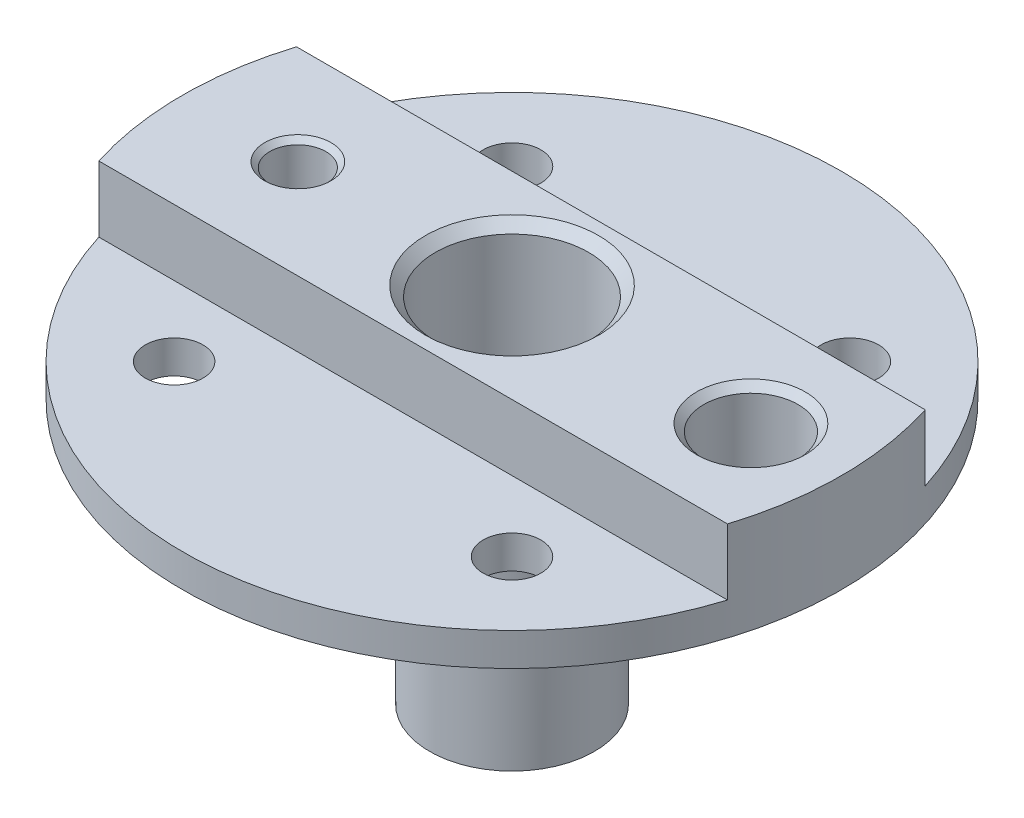
SolidWorks part; units mm, degrees
other "Markup1"
sketch "Sketch15" plane through (38, 45, 38) normal (0.9687, 0.1305, 0.2113) x (0.2474, -0.4357, -0.8654)
material "1.4305 (X8CrNiS18-9)"
ref_plane "Ebene vorne" through (0, 0, 0) normal (0, 0, 1) x (1, 0, 0)
ref_plane "Ebene oben" through (0, 0, 0) normal (0, 1, 0) x (1, 0, 0)
ref_plane "Ebene rechts" through (0, 0, 0) normal (1, 0, 0) x (0, 0, -1)
sketch "Sketch1" plane through (0, 0, 0) normal (0, 0, 1) x (1, 0, 0)
  line L0 (0, 0) -> (0, 46.1077) construction
  line L1 (-40, 44) -> (0, 44)
  line L2 (0, 8) -> (-7.5, 8)
  line L3 (-7.5, 8) -> (-7.5, 0)
  line L4 (-7.5, 0) -> (-10, 0)
  line L5 (-10, 0) -> (-10, 13)
  line L6 (-10, 13) -> (-10.1, 13)
  line L7 (-10.1, 13) -> (-10.1, 17)
  line L8 (-10.1, 17) -> (-9, 17)
  line L9 (-9, 17) -> (-9, 20)
  line L10 (-9, 20) -> (-12, 20)
  line L11 (-12, 20) -> (-12, 30)
  line L12 (-12, 30) -> (-14, 30)
  line L13 (-14, 30) -> (-14, 32)
  line L14 (-14, 32) -> (-40, 32)
  line L15 (-40, 32) -> (-40, 44)
  line L16 (0, 44) -> (0, 8)
  point P12 (-10.5, 20)
  point P20 (-9.55, 17)
  dimension "D1" = 20.2
  dimension "D2" = 20
  dimension "D3" = 18
  dimension "D4" = 2
  dimension "D5" = 2
  dimension "D6" = 40
  dimension "D7" = 12
  dimension "D8" = 12
  dimension "D9" = 1.5
  dimension "D10" = 24
  dimension "D11" = 3
  dimension "D12" = 4
  dimension "D13" = 8
  dimension "D14" = 17
revolve "Revolve1" add sketch "Sketch1" angle 360 about L0
hole_wizard "G1/2 Tapped Hole1" positions "Sketch2" profile "Sketch3" tap size "G1/2" standard "DIN"
sketch "Sketch2" plane through (0, 44, 0) normal (0, 1, 0) x (1, 0, 0)
  point P0 (0, 0)
sketch "Sketch3" plane through (0, 44, 0) normal (1, 0, 0) x (0, 0, 1)
  line L0 (0, 0) -> (0, 26.0373)
  line L1 (0, 26.0373) -> (9.3155, 20.44)
  line L2 (9.3155, 20.44) -> (9.3155, 1.187)
  line L3 (9.3155, 1.187) -> (10.5025, 0)
  line L5 (10.5025, 0) -> (0, 0)
  line L6 (-9.3155, 1.187) -> (-10.5025, 0) construction
  line L10 (0, 26.0373) -> (-9.3155, 20.44) construction
  line L11 (0, -6.35) -> (0, 107.95) construction
  dimension "Tap Drill Dia." = 18.631
  dimension "Tap Drill Depth" = 20.44
  dimension "Near C'Sink Dia." = 21.005
  dimension "Near C'Sink Angle" = 90
  dimension "Drill Angle" = 118
cosmetic thread "Hole Thread1" parameters "D1"=15, "D2"=20.955
ref_plane "Plane1" through (10.1, 0, 0) normal (1, 0, 0) x (0, 0, -1)
sketch "Sketch4" plane through (10.1, 0, 0) normal (1, 0, 0) x (0, 0, -1)
  line L0 (0, 17) -> (0, 13) construction
  line L1 (10.1, 17) -> (-10.1, 17) construction
  line L2 (-10, 13) -> (10, 13) construction
  line L3 (2, 17) -> (2, 13)
  line L4 (-2, 17) -> (-2, 13)
  arc A0 (2, 17) -> (-2, 17) centre (0, 17) ccw
  arc A1 (-2, 13) -> (2, 13) centre (0, 13) ccw
  point P6 (0, 15)
  dimension "D1" = 2
extrude "Cut-Extrude1" cut sketch "Sketch4" against normal blind 1
pattern_circular "CirPattern1" count 8 over 360 about axis through (0, 0, 0) along (0, 1, 0) of "Cut-Extrude1"
hole_wizard "G1/4 Tapped Hole1" positions "Sketch5" profile "Sketch6" tap size "G1/4" standard "DIN" end condition through all
sketch "Sketch5" plane through (0, 44, 0) normal (0, 1, 0) x (1, 0, 0)
  line L0 (0, 0) -> (29, 0) construction
  point P0 (29, 0)
  dimension "D1" = 29
sketch "Sketch6" plane through (29, 44, 0) normal (1, 0, 0) x (0, 0, 1)
  line L0 (0, 0) -> (0, 44)
  line L1 (0, 44) -> (5.7225, 44)
  line L2 (5.7225, 44) -> (5.7225, 0.881)
  line L3 (5.7225, 0.881) -> (6.6035, 0)
  line L5 (6.6035, 0) -> (0, 0)
  line L6 (-5.7225, 0.881) -> (-6.6035, 0) construction
  line L11 (0, -6.35) -> (0, 107.95) construction
  dimension "Thru Tap Drill Dia." = 11.445
  dimension "Thru Tap Drill Depth" = 44
  dimension "Near C'Sink Dia." = 13.207
  dimension "Near C'Sink Angle" = 90
cosmetic thread "Hole Thread2" parameters "D2"=13.157
hole_wizard "M6 Clearance Hole1" positions "Sketch7" profile "Sketch8" hole size "M6" standard "DIN" end condition through all
sketch "Sketch7" plane through (0, 44, 0) normal (0, 1, 0) x (1, 0, 0)
  line L0 (0, 0) -> (16.0639, 0) construction
  line L2 (0, 0) -> (20.5061, 20.5061) construction
  point P0 (20.5061, 20.5061)
  dimension "D1" = 29
  dimension "D2" = 45
sketch "Sketch8" plane through (20.5061, 44, -20.5061) normal (1, 0, 0) x (0, 0, 1)
  line L0 (0, 0) -> (0, 44)
  line L1 (0, 44) -> (3.5, 44)
  line L2 (3.5, 44) -> (3.5, 0.025)
  line L3 (3.5, 0.025) -> (3.525, 0)
  line L5 (3.525, 0) -> (0, 0)
  line L6 (-3.5, 0.025) -> (-3.525, 0) construction
  line L11 (0, -6.35) -> (0, 107.95) construction
  dimension "Thru Hole Dia." = 7
  dimension "Thru Hole Depth" = 44
  dimension "Near C'Sink Dia." = 7.05
  dimension "Near C'Sink Angle" = 90
pattern_circular "CirPattern2" count 4 over 360 about axis through (0, 0, 0) along (0, 1, 0) of "M6 Clearance Hole1"
hole_wizard "Ø2.5 (2.5) Diameter Hole1" positions "Sketch11" profile "Sketch12" hole size "Ø2.5" standard "DIN" end condition through all
sketch "Sketch11" plane through (0, 8, 0) normal (0, -1, 0) x (-1, 0, 0)
  point P0 (6, 0)
  dimension "D1" = 6
sketch "Sketch12" plane through (-6, 8, 0) normal (1, 0, 0) x (0, 0, -1)
  line L0 (0, 0) -> (0, 36)
  line L1 (0, 36) -> (1.25, 36)
  line L2 (1.25, 36) -> (1.25, 0.025)
  line L3 (1.25, 0.025) -> (1.275, 0)
  line L5 (1.275, 0) -> (0, 0)
  line L6 (-1.25, 0.025) -> (-1.275, 0) construction
  line L11 (0, -6.35) -> (0, 107.95) construction
  dimension "Thru Hole Dia." = 2.5
  dimension "Thru Hole Depth" = 36
  dimension "Near C'Sink Dia." = 2.55
  dimension "Near C'Sink Angle" = 90
pattern_circular "CirPattern3" count 8 over 360 about axis through (0, 0, 0) along (0, 1, 0) of "Ø2.5 (2.5) Diameter Hole1"
hole_wizard "M8 Tapped Hole2" positions "Sketch13" profile "Sketch14" tap size "M8" standard "DIN" end condition through all
sketch "Sketch13" plane through (0, 8, 0) normal (0, -1, 0) x (-1, 0, 0)
  point P0 (0, 0)
sketch "Sketch14" plane through (0, 8, 0) normal (1, 0, 0) x (0, 0, -1)
  line L0 (0, 0) -> (0, 36)
  line L1 (0, 36) -> (3.4, 36)
  line L2 (3.4, 36) -> (3.4, 0.625)
  line L3 (3.4, 0.625) -> (4.025, 0)
  line L5 (4.025, 0) -> (0, 0)
  line L6 (-3.4, 0.625) -> (-4.025, 0) construction
  line L11 (0, -6.35) -> (0, 107.95) construction
  dimension "Thru Tap Drill Dia." = 6.8
  dimension "Thru Tap Drill Depth" = 36
  dimension "Near C'Sink Dia." = 8.05
  dimension "Near C'Sink Angle" = 90
cosmetic thread "Hole Thread4" parameters "D2"=8
hole_wizard "M8 Tapped Hole3" positions "Sketch16" profile "Sketch17" tap size "M8" standard "DIN"
sketch "Sketch16" plane through (0, 44, 0) normal (0, 1, 0) x (1, 0, 0)
  line L0 (0, 0) -> (-26, 0) construction
  point P0 (-26, 0)
  dimension "D1" = 26
sketch "Sketch17" plane through (-26, 44, 0) normal (1, 0, 0) x (0, 0, 1)
  line L0 (0, 0) -> (0, 21.7929)
  line L1 (0, 21.7929) -> (3.4, 19.75)
  line L2 (3.4, 19.75) -> (3.4, 0.625)
  line L3 (3.4, 0.625) -> (4.025, 0)
  line L5 (4.025, 0) -> (0, 0)
  line L6 (-3.4, 0.625) -> (-4.025, 0) construction
  line L10 (0, 21.7929) -> (-3.4, 19.75) construction
  line L11 (0, -6.35) -> (0, 107.95) construction
  dimension "Tap Drill Dia." = 6.8
  dimension "Tap Drill Depth" = 19.75
  dimension "Near C'Sink Dia." = 8.05
  dimension "Near C'Sink Angle" = 90
  dimension "Drill Angle" = 118
cosmetic thread "Hole Thread5" parameters "D1"=16, "D2"=8
sketch "Sketch18" plane through (0, 44, 0) normal (0, 1, 0) x (1, 0, 0)
  line L0 (0, 0) -> (-59.8395, 0) construction
  line L1 (-114.5543, 68.9757) -> (114.5543, 68.9757)
  line L2 (-114.5543, 68.9757) -> (-114.5543, 12)
  line L3 (-114.5543, 12) -> (114.5543, 12)
  line L4 (114.5543, 68.9757) -> (114.5543, 12)
  line L5 (-114.5543, 68.9757) -> (114.5543, 12) construction
  line L6 (-114.5543, 12) -> (114.5543, 68.9757) construction
  line L11 (-114.5543, -12) -> (114.5543, -68.9757) construction
  line L12 (-114.5543, -68.9757) -> (114.5543, -12) construction
  line L13 (114.5543, -68.9757) -> (114.5543, -12)
  line L14 (-114.5543, -12) -> (114.5543, -12)
  line L15 (-114.5543, -68.9757) -> (-114.5543, -12)
  line L16 (-114.5543, -68.9757) -> (114.5543, -68.9757)
  point P0 (0, 40.4878)
  point P7 (0, 43.1355)
  point P13 (0, -40.4878)
  dimension "10" = 12
extrude "Cut-Extrude2" cut sketch "Sketch18" against normal offset from surface (8 mm away) 4 up to face at (-26, 32, 3.4)
